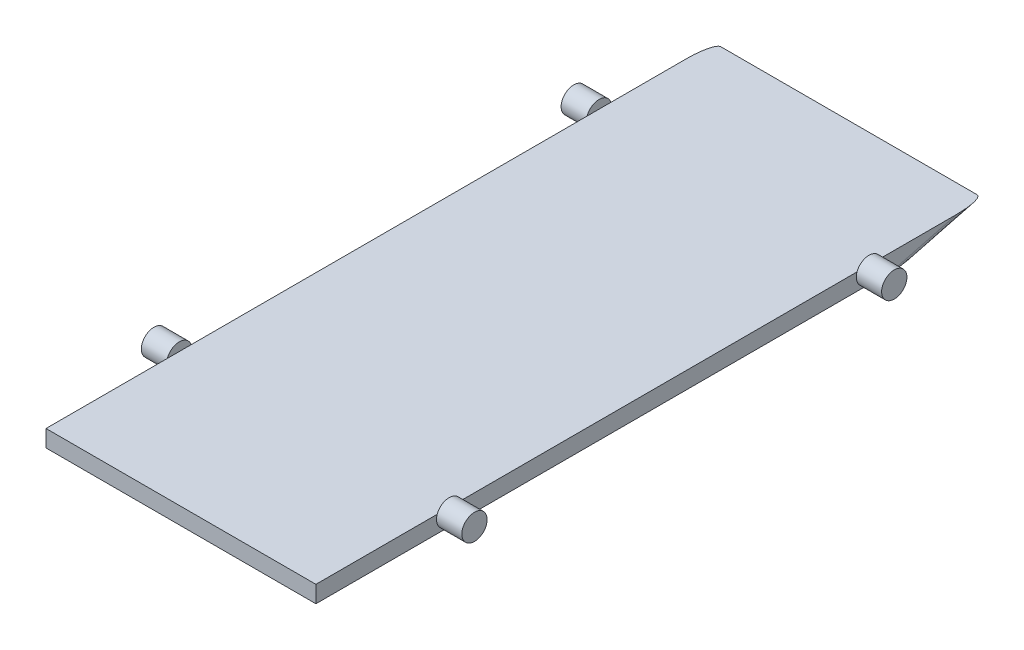
SolidWorks part; units mm, degrees
ref_plane "Front Plane" through (0, 0, 0) normal (0, 0, 1) x (1, 0, 0)
ref_plane "Top Plane" through (0, 0, 0) normal (0, 1, 0) x (1, 0, 0)
ref_plane "Right Plane" through (0, 0, 0) normal (1, 0, 0) x (0, 0, -1)
sketch "Sketch1" plane through (0, 0, 0) normal (0, 1, 0) x (1, 0, 0)
  line L1 (-40, 99) -> (40, 99)
  line L2 (-40, 99) -> (-40, -99)
  line L3 (-40, -99) -> (40, -99)
  line L4 (40, 99) -> (40, -99)
  line L5 (-40, 99) -> (40, -99) construction
  line L6 (-40, -99) -> (40, 99) construction
  point P0 (0, 0)
  dimension "D1" = 198
  dimension "D2" = 80
extrude "Boss-Extrude1" add sketch "Sketch1" along normal blind 5
sketch "Sketch2" plane through (-40, 0, 0) normal (-1, 0, 0) x (0, 0, 1)
  line L0 (99, 0) -> (-99, 0)
  line L1 (-64.9289, 5) -> (-99, 5)
  line L2 (-99, 5) -> (99, 5) construction
  line L3 (99, 5) -> (59.5, 5)
  line L4 (-99, 2.5) -> (-64.9289, 2.5) construction
  line L5 (-99, 5) -> (-99, 0) construction
  line L6 (-64.9289, 2.5) -> (-64.9289, 5) construction
  circle A0 centre (-64.9289, 3.75) radius 3.75
  circle A1 centre (59.5, 3.75) radius 3.75
  point P3 (0, 0)
  dimension "D3" = 7.5
  dimension "D4" = 7.5
  dimension "D1" = 34.0711
  dimension "D2" = 39.5
extrude "Boss-Extrude2" add sketch "Sketch2" along normal blind 7.5 contours L5 A0 | L3 A1 L5 | L5 A1 L3
mirror "Mirror1" about plane through (0, 0, 0) normal (1, 0, 0) of "Boss-Extrude2"
sketch "Sketch3" plane through (-40, 0, 0) normal (-1, 0, 0) x (0, 0, 1)
  line L0 (-99, 5) -> (-72.9325, -1.7591)
  line L1 (-72.9325, -1.7591) -> (-103.7993, -1.7591)
  line L2 (-103.7993, -1.7591) -> (-99, 5)
  point P3 (-105.751, -4.5078)
  point P5 (-72.9325, -1.7591)
  dimension "D1" = 165.464
  dimension "D2" = 125.377
  dimension "D3" = 30.8668
extrude "Cut-Extrude1" cut sketch "Sketch3" against normal through all
fillet "Fillet2" radius 2 2 edges at (40, 2.5, -89.3584) (-40, 2.5, -89.3584)
